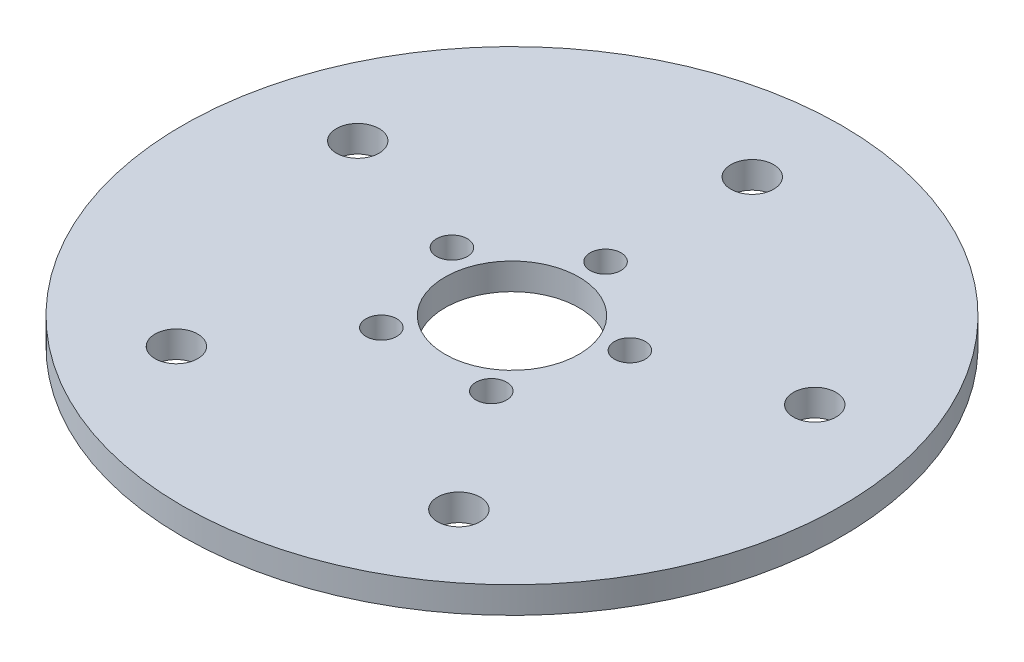
SolidWorks part; units mm, degrees
material "6061 Alloy"
ref_plane "Front Plane" through (0, 0, 0) normal (0, 0, 1) x (1, 0, 0)
ref_plane "Top Plane" through (0, 0, 0) normal (0, 1, 0) x (1, 0, 0)
ref_plane "Right Plane" through (0, 0, 0) normal (1, 0, 0) x (0, 0, -1)
sketch "Sketch1" plane through (0, 807.1164, 0) normal (0, 1, 0) x (-1, 0, 0)
  circle A0 centre (0, 0) radius 39.37
  dimension "D1" = 78.74
extrude "Boss-Extrude1" add sketch "Sketch1" against normal blind 3.175
sketch "Sketch2" plane through (0, 807.1164, 0) normal (0, 1, 0) x (1, 0, 0)
  line L0 (0, 0) -> (0, 11.176) construction
  line L1 (0, 0) -> (0, 28.702) construction
  circle A0 centre (0, 0) radius 8.001
  circle A1 centre (0, 0) radius 39.37 construction
  circle A2 centre (0, 11.176) radius 1.8415
  circle A3 centre (10.629, 3.4536) radius 1.8415
  circle A4 centre (6.5691, -9.0416) radius 1.8415
  circle A5 centre (-6.5691, -9.0416) radius 1.8415
  circle A6 centre (-10.629, 3.4536) radius 1.8415
  circle A7 centre (0, 28.702) radius 2.5527
  circle A8 centre (27.2972, 8.8694) radius 2.5527
  circle A9 centre (16.8706, -23.2204) radius 2.5527
  circle A10 centre (-16.8706, -23.2204) radius 2.5527
  circle A11 centre (-27.2972, 8.8694) radius 2.5527
  point P27 (0, 0)
  dimension "D1" = 16.002
  dimension "D2" = 3.683
  dimension "D6" = 5.1054
  dimension "D3" = 11.176
  dimension "D5" = 28.702
  dimension "D4" = 5
  dimension "D7" = 5
extrude "Cut-Extrude1" cut sketch "Sketch2" against normal through all
